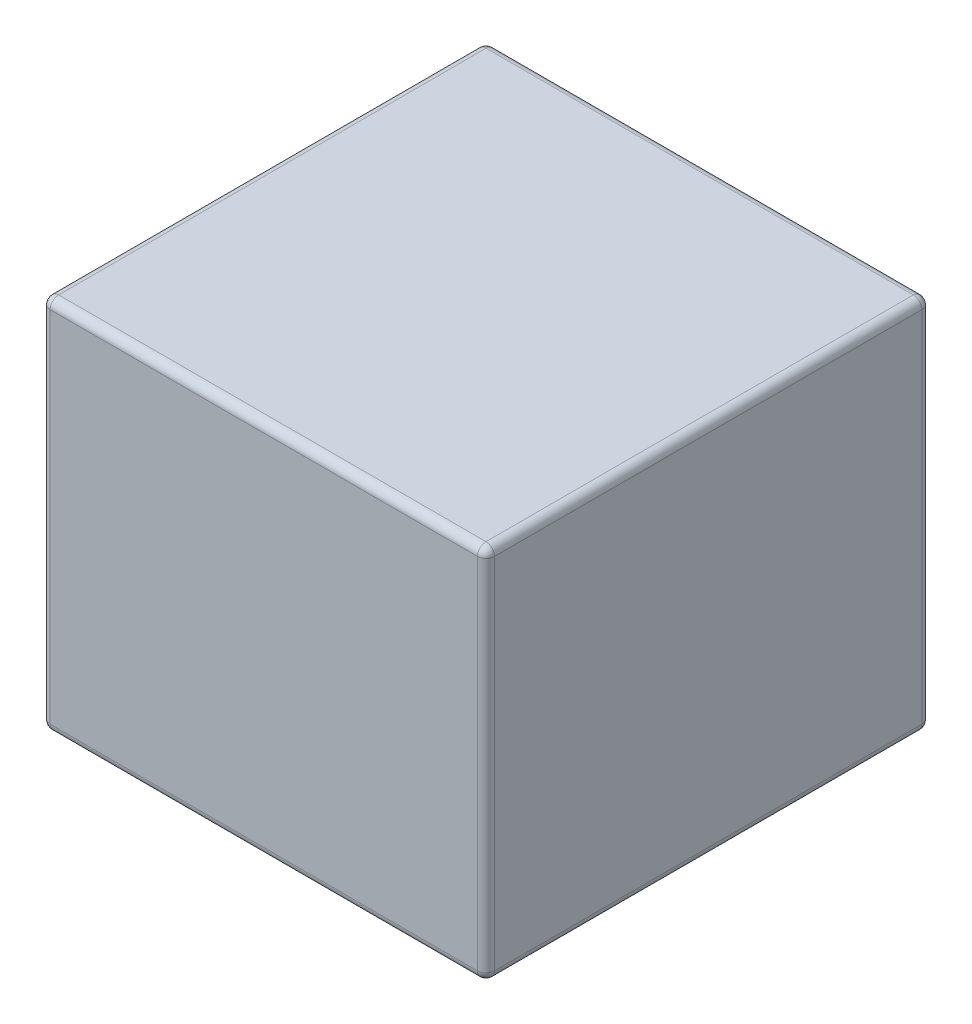
SolidWorks part; units mm, degrees
ref_plane "Front Plane" through (0, 0, 0) normal (0, 0, 1) x (1, 0, 0)
ref_plane "Top Plane" through (0, 0, 0) normal (0, 1, 0) x (1, 0, 0)
ref_plane "Right Plane" through (0, 0, 0) normal (1, 0, 0) x (0, 0, -1)
sketch "Sketch1" plane through (0, 0, 0) normal (0, 1, 0) x (1, 0, 0)
  line L1 (0, 0) -> (330.2, 0)
  line L2 (0, 0) -> (0, 330.2)
  line L3 (0, 330.2) -> (330.2, 330.2)
  line L4 (330.2, 0) -> (330.2, 330.2)
  dimension "D1" = 330.2
  dimension "D2" = 330.2
extrude "Boss-Extrude1" add sketch "Sketch1" along normal blind 279.4
fillet "Fillet1" radius 6.35 12 edges at (0, 0, -165.1) (0, 139.7, -330.2) (165.1, 0, -330.2) (330.2, 139.7, -330.2) (330.2, 0, -165.1) (0, 139.7, 0) (330.2, 139.7, 0) (165.1, 0, 0) (165.1, 279.4, -330.2) (330.2, 279.4, -165.1) (165.1, 279.4, 0) (0, 279.4, -165.1)
